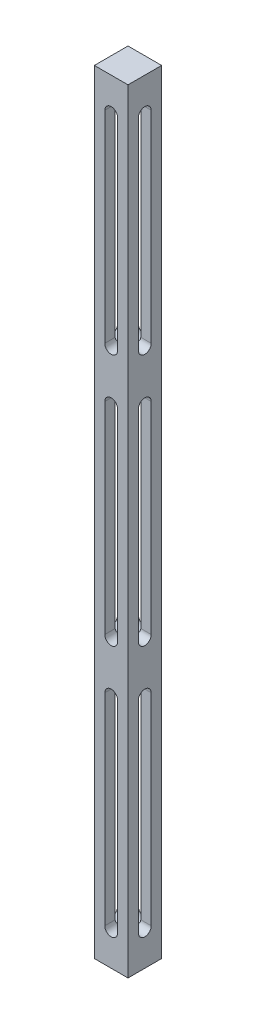
SolidWorks part; units mm, degrees
material "6061-T6 (SS)"
ref_plane "Front Plane" through (0, 0, 0) normal (0, 0, 1) x (1, 0, 0)
ref_plane "Top Plane" through (0, 0, 0) normal (0, 1, 0) x (1, 0, 0)
ref_plane "Right Plane" through (0, 0, 0) normal (1, 0, 0) x (0, 0, -1)
sketch "Sketch1" plane through (0, 0, 0) normal (0, 1, 0) x (1, 0, 0)
  line L1 (-6.35, -6.35) -> (6.35, -6.35)
  line L2 (-6.35, -6.35) -> (-6.35, 6.35)
  line L3 (-6.35, 6.35) -> (6.35, 6.35)
  line L4 (6.35, -6.35) -> (6.35, 6.35)
  line L5 (-6.35, -6.35) -> (6.35, 6.35) construction
  line L6 (-6.35, 6.35) -> (6.35, -6.35) construction
  point P0 (0, 0)
  dimension "D1" = 12.7
  dimension "D2" = 12.7
extrude "Boss-Extrude1" add sketch "Sketch1" along normal blind 292.1
sketch "Sketch2" plane through (0, 0, -6.35) normal (0, 0, -1) x (-1, 0, 0)
  line L0 (-6.35, 292.1) -> (6.35, 292.1) construction
  line L1 (-2.413, 279.4) -> (-2.413, 203.2)
  line L2 (2.413, 279.4) -> (2.413, 203.2)
  arc A0 (2.413, 279.4) -> (-2.413, 279.4) centre (0, 279.4) ccw
  arc A2 (-2.413, 203.2) -> (2.413, 203.2) centre (0, 203.2) ccw
  dimension "D1" = 12.7
  dimension "D2" = 2.413
  dimension "D3" = 76.2
extrude "Cut-Extrude1" cut sketch "Sketch2" against normal through all
sketch "Sketch3" plane through (6.35, 0, 0) normal (1, 0, 0) x (0, 0, -1)
  line L0 (-2.413, 279.4) -> (-2.413, 203.2)
  line L1 (2.413, 279.4) -> (2.413, 203.2)
  line L2 (-6.35, 292.1) -> (6.35, 292.1) construction
  line L3 (6.35, 292.1) -> (6.35, 0) construction
  arc A0 (2.413, 279.4) -> (-2.413, 279.4) centre (0, 279.4) ccw
  arc A1 (-2.413, 203.2) -> (2.413, 203.2) centre (0, 203.2) ccw
  dimension "D4" = 2.413
  dimension "D1" = 12.7
  dimension "D2" = 76.2
  dimension "D3" = 6.35
extrude "Cut-Extrude2" cut sketch "Sketch3" against normal through all
pattern_linear "LPattern1" count 3 spacing 95.25 along (0, -1, 0) of "Cut-Extrude1", "Cut-Extrude2"
